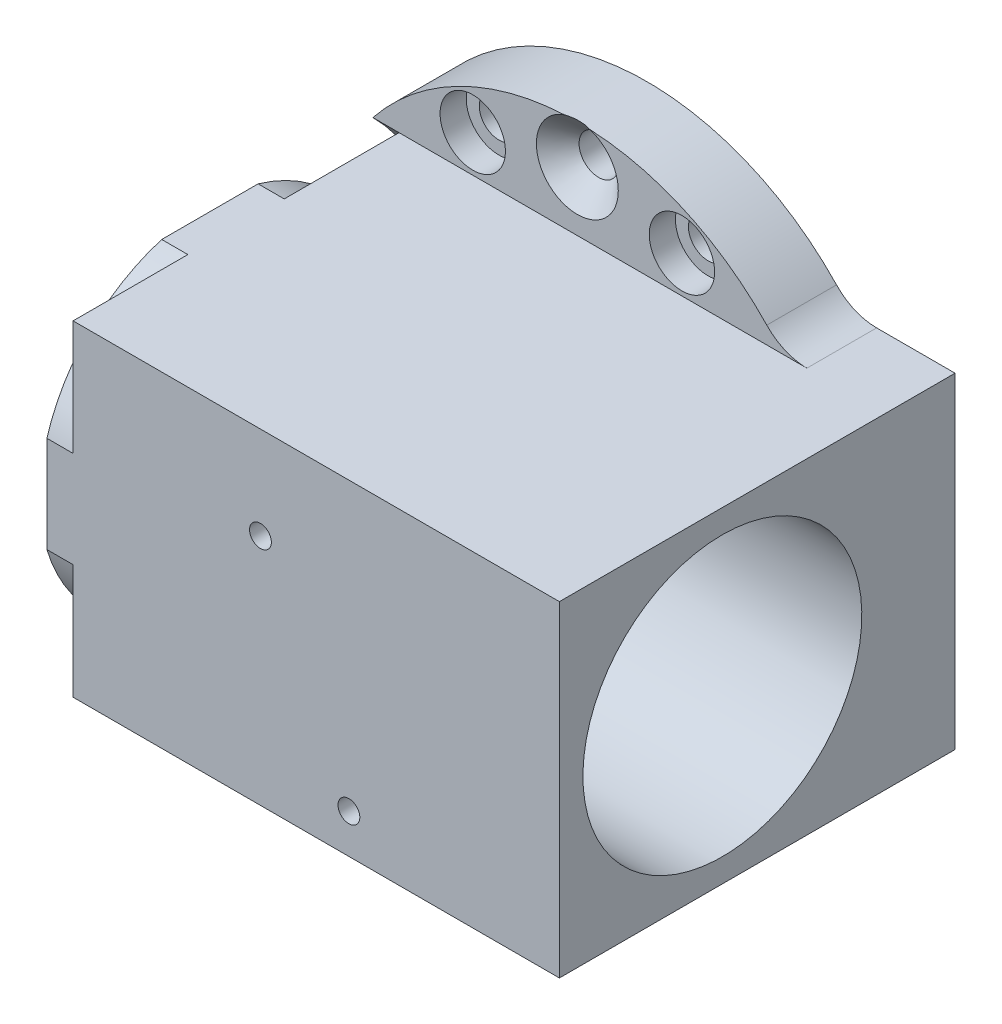
SolidWorks part; units mm, degrees
ref_plane "Front Plane" through (0, 0, 0) normal (0, 0, 1) x (1, 0, 0)
ref_plane "Top Plane" through (0, 0, 0) normal (0, 1, 0) x (1, 0, 0)
ref_plane "Right Plane" through (0, 0, 0) normal (1, 0, 0) x (0, 0, -1)
ref_plane "Plane1" through (0, 0, 8) normal (0, 0, 1) x (1, 0, 0)
sketch "Sketch1" plane through (0, 0, 8) normal (0, 0, 1) x (1, 0, 0)
  line L0 (-23.4587, 18.7) -> (-23.4587, -18.7)
  line L1 (23.4587, -18.7) -> (35.3413, -18.7)
  line L2 (35.3413, -18.7) -> (35.3413, 18.7)
  line L3 (35.3413, 18.7) -> (23.4587, 18.7)
  arc A0 (-23.4587, -18.7) -> (23.4587, -18.7) centre (0, 0) ccw
  arc A1 (23.4587, 18.7) -> (-23.4587, 18.7) centre (0, 0) ccw
extrude "Boss-Extrude1" add sketch "Sketch1" against normal blind 8
ref_plane "Plane2" through (-23.4587, 0, 0) normal (-1, 0, 0) x (0, -1, 0)
ref_plane "Plane3" through (-20.4587, 0, 0) normal (1, 0, 0) x (0, 0, -1)
sketch "Sketch3" plane through (-20.4587, 0, 0) normal (1, 0, 0) x (0, 0, -1)
  line L0 (-8, 18.7) -> (-8, -18.7)
  arc A0 (-8, -18.7) -> (-8, 18.7) centre (-26.7, 0) ccw
extrude "Cut-Extrude1" cut sketch "Sketch3" against normal up to surface up to plane "Plane2"
sketch "Sketch4" plane through (0, 0, 8) normal (0, 0, 1) x (1, 0, 0)
  line L0 (-20.4587, -18.7) -> (-20.4587, 18.7)
  line L1 (-20.4587, 18.7) -> (35.3413, 18.7)
  line L2 (35.3413, 18.7) -> (35.3413, -18.7)
  line L3 (35.3413, -18.7) -> (-20.4587, -18.7)
extrude "Boss-Extrude2" add sketch "Sketch4" along normal blind 37.4
sketch "Sketch5" plane through (-20.4587, 0, 0) normal (-1, 0, 0) x (0, 0, 1)
  line L0 (21.1719, 18.7) -> (45.4, 18.7)
  line L1 (45.4, 18.7) -> (45.4, -18.7)
  line L2 (45.4, -18.7) -> (21.1719, -18.7)
  arc A0 (21.1719, -18.7) -> (21.1719, 18.7) centre (26.7, 0) cw
extrude "Boss-Extrude3" add sketch "Sketch5" along normal blind 3
sketch "Sketch6" plane through (-23.4587, 0, 0) normal (-1, 0, 0) x (0, 0, 1)
  line L0 (45.4, -18.7) -> (45.4, -5.5281)
  line L1 (32.2281, -18.7) -> (45.4, -18.7)
  arc A0 (45.4, -5.5281) -> (32.2281, -18.7) centre (26.7, 0) cw
extrude "Cut-Extrude2" cut sketch "Sketch6" against normal blind 3
sketch "Sketch7" plane through (-23.4587, 0, 0) normal (-1, 0, 0) x (0, 0, 1)
  line L0 (45.4, 18.7) -> (32.2281, 18.7)
  line L1 (45.4, 5.5281) -> (45.4, 18.7)
  arc A0 (32.2281, 18.7) -> (45.4, 5.5281) centre (26.7, 0) cw
extrude "Cut-Extrude3" cut sketch "Sketch7" against normal blind 3
ref_plane "Plane4" through (0, 0, 26.7) normal (0, 0, 1) x (1, 0, 0)
sketch "Sketch8" plane through (0, 0, 26.7) normal (0, 0, 1) x (1, 0, 0)
  line L0 (-23.4587, 15.8686) -> (-23.4587, 0)
  line L1 (-23.4587, 0) -> (35.3413, 0)
  line L2 (35.3413, 0) -> (35.3413, 15.8687)
  line L3 (35.3413, 15.8687) -> (9.9413, 15.8687)
  line L4 (9.9413, 15.8687) -> (9.9413, 13.5)
  line L5 (9.9413, 13.5) -> (1.9413, 13.5)
  line L6 (1.9413, 13.5) -> (1.9413, 15.8686)
  line L7 (1.9413, 15.8686) -> (-23.4587, 15.8686)
  line L8 (-23.4587, 0) -> (35.3413, 0) construction
revolve "Cut-Revolve1" cut sketch "Sketch8" angle 360 about L8
hole_wizard "CSK for #8 Flat Head Machine Screw (100)1" positions "Sketch10" profile "Sketch9" countersink size "#8" standard "ANSI Inch"
sketch "Sketch10" plane through (0, 0, 8) normal (0, 0, 1) x (1, 0, 0)
  point P0 (0, 25.5)
  point P1 (0, -25.5)
sketch "Sketch9" plane through (0, 25.5, 8) normal (1, 0, 0) x (0, -1, 0)
  line L0 (0, 0) -> (0, 8)
  line L1 (0, 8) -> (2.25, 8)
  line L2 (2.25, 8) -> (2.25, 2.45)
  line L3 (2.25, 2.45) -> (4.7, 0)
  line L5 (4.7, 0) -> (0, 0)
  line L6 (-2.25, 2.45) -> (-4.7, 0) construction
  line L11 (0, -6.35) -> (0, 107.95) construction
  dimension "Thru Hole Dia." = 4.5
  dimension "Thru Hole Depth" = 8
  dimension "Near C'Sink Dia." = 9.4
  dimension "Near C'Sink Angle" = 90
hole_wizard "#4 Clearance Hole1" positions "Sketch12" profile "Sketch11" hole size "#4" standard "ANSI Inch"
sketch "Sketch12" plane through (0, -18.7, 0) normal (0, -1, 0) x (-1, 0, 0)
  point P0 (12.4587, -39.4)
  point P1 (-29.4413, -39.4)
  point P2 (-29.4413, -5.9)
sketch "Sketch11" plane through (-12.4587, -18.7, 39.4) normal (1, 0, 0) x (0, 0, -1)
  line L0 (0, 0) -> (0, 6)
  line L1 (0, 6) -> (1.65, 6)
  line L2 (1.65, 6) -> (1.65, 0)
  line L5 (1.65, 0) -> (0, 0)
  line L10 (0, 6) -> (-1.65, 6) construction
  line L11 (0, -6.35) -> (0, 107.95) construction
  dimension "Hole Dia." = 3.3
  dimension "Hole Depth" = 6
  dimension "Drill Angle" = 180
hole_wizard "CBORE for #8 Binding Head Machine Screw1" positions "Sketch14" profile "Sketch13" counterbore size "#8" standard "ANSI Inch"
sketch "Sketch14" plane through (0, 0, 8) normal (0, 0, 1) x (1, 0, 0)
  point P0 (12, 22.95)
  point P1 (-12, 22.95)
  point P2 (-12, -22.95)
  point P3 (12, -22.95)
sketch "Sketch13" plane through (12, 22.95, 8) normal (1, 0, 0) x (0, -1, 0)
  line L0 (0, 0) -> (0, 8)
  line L1 (0, 8) -> (2.25, 8)
  line L3 (2.25, 8) -> (2.25, 3)
  line L4 (2.25, 3) -> (3.75, 3)
  line L5 (3.75, 3) -> (3.75, 0)
  line L7 (3.75, 0) -> (0, 0)
  line L11 (0, -6.35) -> (0, 107.95) construction
  dimension "Thru Hole Dia." = 4.5
  dimension "Thru Hole Depth" = 8
  dimension "C'Bore Dia." = 7.5
  dimension "C'Bore Depth" = 3
hole_wizard "#2 Clearance Hole1" positions "Sketch16" profile "Sketch15" hole size "#2" standard "ANSI Inch"
sketch "Sketch16" plane through (0, 0, 45.4) normal (0, 0, 1) x (1, 0, 0)
  point P0 (-0.8087, 14.63)
sketch "Sketch15" plane through (-0.8087, 14.63, 45.4) normal (1, 0, 0) x (0, -1, 0)
  line L0 (0, 0) -> (0, 6)
  line L1 (0, 6) -> (1.25, 6)
  line L2 (1.25, 6) -> (1.25, 0)
  line L5 (1.25, 0) -> (0, 0)
  line L10 (0, 6) -> (-1.25, 6) construction
  line L11 (0, -6.35) -> (0, 107.95) construction
  dimension "Hole Dia." = 2.5
  dimension "Hole Depth" = 6
  dimension "Drill Angle" = 180
hole_wizard "#2 Clearance Hole2" positions "Sketch18" profile "Sketch17" hole size "#2" standard "ANSI Inch"
sketch "Sketch18" plane through (0, 0, 45.4) normal (0, 0, 1) x (1, 0, 0)
  point P0 (15.9651, -3.2)
sketch "Sketch17" plane through (15.9651, -3.2, 45.4) normal (1, 0, 0) x (0, -1, 0)
  line L0 (0, 0) -> (0, 3.1573)
  line L1 (0, 3.1573) -> (1.25, 3.1573)
  line L2 (1.25, 3.1573) -> (1.25, 0)
  line L5 (1.25, 0) -> (0, 0)
  line L11 (0, -6.35) -> (0, 107.95) construction
  dimension "Thru Hole Dia." = 2.5
  dimension "Thru Hole Depth" = 3.1573
fillet "Fillet1" radius 6.35 1 edges at (23.4587, 18.7, 4)
sketch "Sketch20" plane through (0, 0, 45.4) normal (0, 0, 1) x (1, 0, 0)
  line L0 (35.3413, 18.7) -> (-20.4587, 18.7) construction
  line L1 (-20.4587, -18.7) -> (35.3413, -18.7) construction
  line L2 (-23.4587, 18.7) -> (-23.4587, 5.5281) construction
  point P0 (1.0413, 8.0737)
  point P1 (11.1917, -14.199)
  dimension "D1" = 10.6263
  dimension "D2" = 4.501
  dimension "D3" = 24.4766
  dimension "D4" = 24.5
hole_wizard "M3x0.5 Tapped Hole1" positions "3DSketch1" profile "Sketch23" tap size "M3x0.5" standard "ANSI Metric"
sketch3d "3DSketch1"
  point P0 (1.0413, 8.0737, 45.4)
  point P3 (11.1917, -14.199, 45.4)
sketch "Sketch23" plane through (1.0413, 8.0737, 45.4) normal (1, 0, 0) x (0, -1, 0)
  line L0 (0, 0) -> (0, 4.7511)
  line L1 (0, 4.7511) -> (1.25, 4)
  line L2 (1.25, 4) -> (1.25, 0)
  line L5 (1.25, 0) -> (0, 0)
  line L10 (0, 4.7511) -> (-1.25, 4) construction
  line L11 (0, -6.35) -> (0, 107.95) construction
  dimension "Tap Drill Dia." = 2.5
  dimension "Tap Drill Depth" = 4
  dimension "Drill Angle" = 118
cosmetic thread "Hole Thread1" parameters "D1"=4, "D2"=3
cosmetic thread "Hole Thread2" parameters "D1"=4, "D2"=3
fillet "Fillet2" radius 6.35 1 edges at (23.4587, -18.7, 4)
sketch "草图1" plane through (35.3413, 0, 0) normal (1, 0, 0) x (0, 0, -1)
  circle A2 centre (-26.7, 0) radius 16
  dimension "D1" = 32
extrude "切除-拉伸1" cut sketch "草图1" against normal up to surface (25.4 mm away) up to face at (9.9413, 13.5, 26.7)
sketch "草图2" plane through (-23.4587, 0, 0) normal (-1, 0, 0) x (0, 0, 1)
  circle A0 centre (26.7, 0) radius 16
  dimension "D1" = 32
extrude "切除-拉伸2" cut sketch "草图2" against normal up to surface (25.4 mm away) up to face at (1.9413, 15.8686, 26.7)
sketch "草图3" plane through (1.9413, 0, 0) normal (-1, 0, 0) x (0, 0, 1)
  circle A0 centre (26.7, 0) radius 13.55
  dimension "D1" = 27.1
extrude "切除-拉伸3" cut sketch "草图3" against normal blind 10
